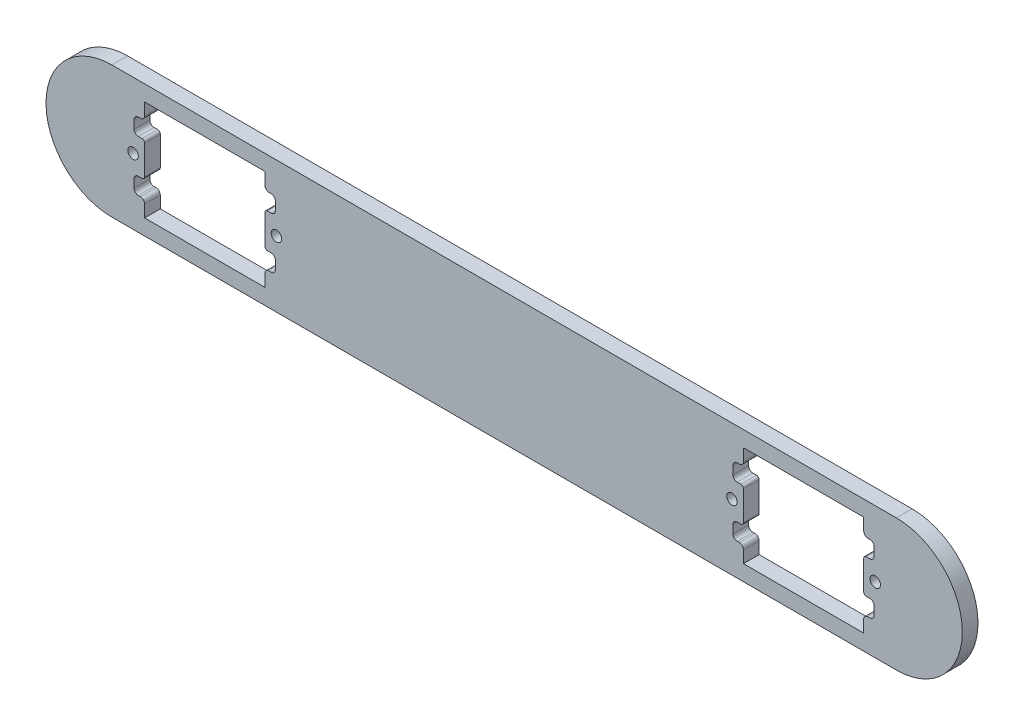
SolidWorks part; units mm, degrees
ref_plane "前视基准面" through (0, 0, 0) normal (0, 0, 1) x (1, 0, 0)
ref_plane "上视基准面" through (0, 0, 0) normal (0, 1, 0) x (1, 0, 0)
ref_plane "右视基准面" through (0, 0, 0) normal (1, 0, 0) x (0, 0, -1)
sketch "草图1" plane through (0, 0, 0) normal (0, 0, 1) x (1, 0, 0)
  line L0 (-75, 0) -> (75, 0) construction
  line L1 (-75, 12.6) -> (75, 12.6)
  line L2 (-75, -12.6) -> (75, -12.6)
  line L3 (0, 0) -> (0, 24.2406) construction
  line L4 (-57.25, 0) -> (-57.25, 14.1552) construction
  line L5 (-68.75, 6.5) -> (-45.75, 6.5)
  line L6 (-68.75, 6.5) -> (-68.75, -6.5)
  line L7 (-68.75, -6.5) -> (-45.75, -6.5)
  line L8 (-45.75, 6.5) -> (-45.75, -6.5)
  line L9 (-68.75, 6.5) -> (-45.75, -6.5) construction
  line L10 (-68.75, -6.5) -> (-45.75, 6.5) construction
  line L11 (68.75, 6.5) -> (68.75, -6.5)
  line L12 (68.75, 6.5) -> (45.75, 6.5)
  line L13 (45.75, 6.5) -> (45.75, -6.5)
  line L14 (68.75, -6.5) -> (45.75, -6.5)
  arc A0 (-75, 12.6) -> (-75, -12.6) centre (-75, 0) ccw
  arc A1 (75, -12.6) -> (75, 12.6) centre (75, 0) ccw
  circle A2 centre (-43.55, 0) radius 1
  circle A3 centre (-70.95, 0) radius 1
  circle A4 centre (-62.5, 0) radius 4 construction
  circle A5 centre (70.95, 0) radius 1
  circle A6 centre (62.5, 0) radius 4 construction
  circle A7 centre (43.55, 0) radius 1
  point P3 (0, 0)
  point P11 (-57.25, 0)
  dimension "D4" = 2
  dimension "D8" = 8
  dimension "D6" = 125
  dimension "D1" = 25.2
  dimension "D2" = 23
  dimension "D3" = 13
  dimension "D5" = 6.25
  dimension "D7" = 27.4
  dimension "D9" = 150
extrude "凸台-拉伸1" add sketch "草图1" along normal mid plane 3
sketch "草图2" plane through (0, 0, 1.5) normal (0, 0, 1) x (1, 0, 0)
  line L0 (44.95, 6.5) -> (44.55, 6.5)
  line L1 (45.75, 6.5) -> (45.75, -6.5) construction
  line L2 (43.75, 5.7) -> (43.75, 4.1)
  line L3 (44.55, 3.3) -> (45.75, 3.3)
  line L5 (68.75, 6.5) -> (45.75, 6.5) construction
  line L6 (45.75, 7.3) -> (45.75, 9.6)
  line L7 (45.75, 9.6) -> (68.75, 9.6)
  line L8 (68.75, 9.6) -> (68.75, 7.3)
  line L9 (57.25, 6.5) -> (57.25, 12.6) construction
  line L10 (75, 12.6) -> (-75, 12.6) construction
  line L11 (69.55, 6.5) -> (69.95, 6.5)
  line L12 (70.75, 5.7) -> (70.75, 4.1)
  line L13 (69.95, 3.3) -> (68.75, 3.3)
  line L14 (45.75, 3.3) -> (45.75, 6.5)
  line L15 (45.75, 6.5) -> (68.75, 6.5)
  line L16 (68.75, 6.5) -> (68.75, 3.3)
  line L17 (45.75, 0) -> (37.6082, 0) construction
  line L18 (44.55, -3.3) -> (45.75, -3.3)
  line L19 (43.75, -5.7) -> (43.75, -4.1)
  line L20 (44.95, -6.5) -> (44.55, -6.5)
  line L21 (45.75, -7.3) -> (45.75, -9.6)
  line L22 (45.75, -9.6) -> (68.75, -9.6)
  line L23 (68.75, -9.6) -> (68.75, -7.3)
  line L24 (69.55, -6.5) -> (69.95, -6.5)
  line L25 (70.75, -5.7) -> (70.75, -4.1)
  line L26 (69.95, -3.3) -> (68.75, -3.3)
  line L27 (68.75, -6.5) -> (68.75, -3.3)
  line L28 (45.75, -6.5) -> (68.75, -6.5)
  line L29 (45.75, -3.3) -> (45.75, -6.5)
  line L30 (0, 0) -> (0, 16.9532) construction
  line L31 (-45.75, 3.3) -> (-45.75, 6.5)
  line L32 (-44.55, 3.3) -> (-45.75, 3.3)
  line L33 (-43.75, 5.7) -> (-43.75, 4.1)
  line L34 (-44.95, 6.5) -> (-44.55, 6.5)
  line L35 (-45.75, 7.3) -> (-45.75, 9.6)
  line L36 (-45.75, 9.6) -> (-68.75, 9.6)
  line L37 (-68.75, 9.6) -> (-68.75, 7.3)
  line L38 (-69.55, 6.5) -> (-69.95, 6.5)
  line L39 (-70.75, 5.7) -> (-70.75, 4.1)
  line L40 (-69.95, 3.3) -> (-68.75, 3.3)
  line L41 (-68.75, 6.5) -> (-68.75, 3.3)
  line L42 (-45.75, 6.5) -> (-68.75, 6.5)
  line L43 (-45.75, -7.3) -> (-45.75, -9.6)
  line L44 (-44.95, -6.5) -> (-44.55, -6.5)
  line L45 (-43.75, -5.7) -> (-43.75, -4.1)
  line L46 (-44.55, -3.3) -> (-45.75, -3.3)
  line L47 (-45.75, -3.3) -> (-45.75, -6.5)
  line L48 (-45.75, -6.5) -> (-68.75, -6.5)
  line L49 (-68.75, -6.5) -> (-68.75, -3.3)
  line L50 (-69.95, -3.3) -> (-68.75, -3.3)
  line L51 (-70.75, -5.7) -> (-70.75, -4.1)
  line L52 (-69.55, -6.5) -> (-69.95, -6.5)
  line L53 (-68.75, -9.6) -> (-68.75, -7.3)
  line L54 (-45.75, -9.6) -> (-68.75, -9.6)
  arc A0 (69.95, 3.3) -> (70.75, 4.1) centre (69.95, 4.1) ccw
  arc A1 (69.95, 6.5) -> (70.75, 5.7) centre (69.95, 5.7) cw
  arc A2 (69.55, 6.5) -> (68.75, 7.3) centre (69.55, 7.3) cw
  arc A3 (45.75, 7.3) -> (44.95, 6.5) centre (44.95, 7.3) cw
  arc A4 (44.55, 6.5) -> (43.75, 5.7) centre (44.55, 5.7) ccw
  arc A5 (43.75, 4.1) -> (44.55, 3.3) centre (44.55, 4.1) ccw
  arc A6 (43.75, -4.1) -> (44.55, -3.3) centre (44.55, -4.1) cw
  arc A7 (44.55, -6.5) -> (43.75, -5.7) centre (44.55, -5.7) cw
  arc A8 (45.75, -7.3) -> (44.95, -6.5) centre (44.95, -7.3) ccw
  arc A9 (69.55, -6.5) -> (68.75, -7.3) centre (69.55, -7.3) ccw
  arc A10 (69.95, -6.5) -> (70.75, -5.7) centre (69.95, -5.7) ccw
  arc A11 (69.95, -3.3) -> (70.75, -4.1) centre (69.95, -4.1) cw
  arc A12 (-43.75, 4.1) -> (-44.55, 3.3) centre (-44.55, 4.1) cw
  arc A13 (-44.55, 6.5) -> (-43.75, 5.7) centre (-44.55, 5.7) cw
  arc A14 (-45.75, 7.3) -> (-44.95, 6.5) centre (-44.95, 7.3) ccw
  arc A15 (-69.55, 6.5) -> (-68.75, 7.3) centre (-69.55, 7.3) ccw
  arc A16 (-69.95, 6.5) -> (-70.75, 5.7) centre (-69.95, 5.7) ccw
  arc A17 (-69.95, 3.3) -> (-70.75, 4.1) centre (-69.95, 4.1) cw
  arc A18 (-45.75, -7.3) -> (-44.95, -6.5) centre (-44.95, -7.3) cw
  arc A19 (-44.55, -6.5) -> (-43.75, -5.7) centre (-44.55, -5.7) ccw
  arc A20 (-43.75, -4.1) -> (-44.55, -3.3) centre (-44.55, -4.1) ccw
  arc A21 (-69.95, -3.3) -> (-70.75, -4.1) centre (-69.95, -4.1) ccw
  arc A22 (-69.95, -6.5) -> (-70.75, -5.7) centre (-69.95, -5.7) cw
  arc A23 (-69.55, -6.5) -> (-68.75, -7.3) centre (-69.55, -7.3) cw
  point P21 (70.75, 3.3)
  point P24 (70.75, 6.5)
  point P27 (68.75, 6.5)
  point P30 (45.75, 6.5)
  point P33 (43.75, 6.5)
  point P36 (43.75, 3.3)
  dimension "D4" = 0.8
  dimension "D1" = 3.2
  dimension "D2" = 2
  dimension "D3" = 3.1
extrude "切除-拉伸1" cut sketch "草图2" against normal blind 3
fillet "圆角1" radius 0.5 8 edges at (-68.75, -3.3, 0) (-68.75, 3.3, 0) (-45.75, -3.3, 0) (-45.75, 3.3, 0) (68.75, -3.3, 0) (68.75, 3.3, 0) (45.75, -3.3, 0) (45.75, 3.3, 0)
